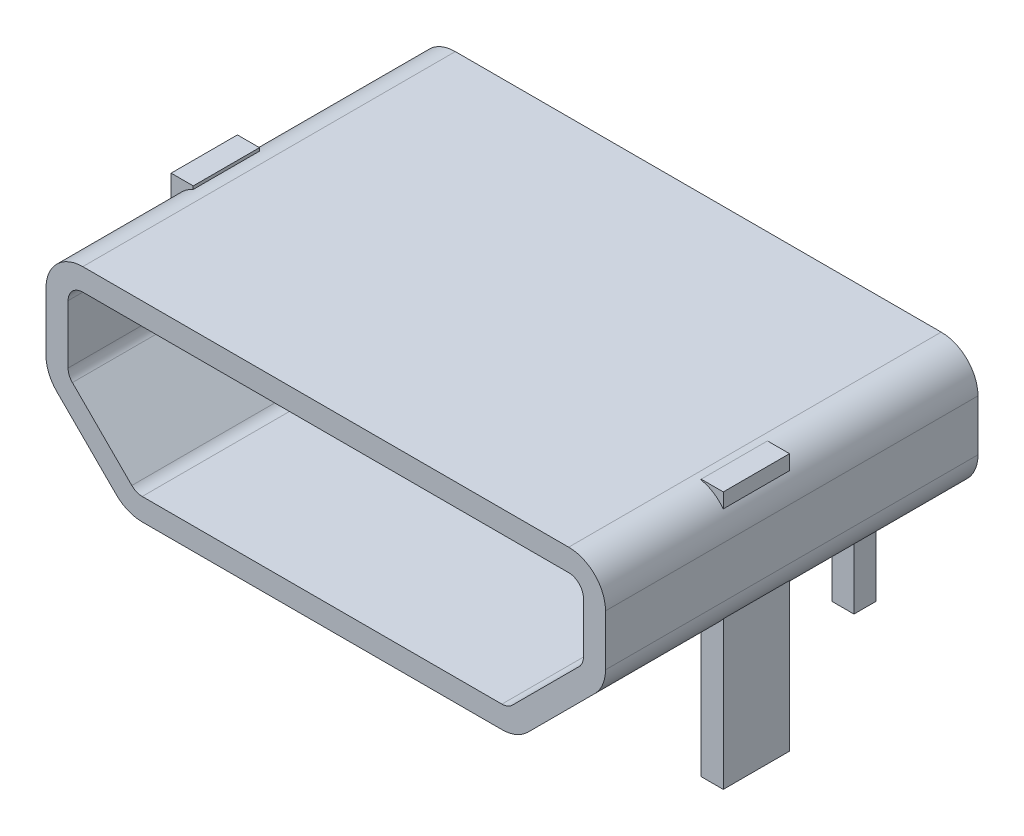
SolidWorks part; units mm, degrees
ref_plane "前视基准面" through (0, 0, 0) normal (0, 0, 1) x (1, 0, 0)
ref_plane "上视基准面" through (0, 0, 0) normal (0, 1, 0) x (1, 0, 0)
ref_plane "右视基准面" through (0, 0, 0) normal (1, 0, 0) x (0, 0, -1)
sketch "草图1" plane through (0, 0, 0) normal (0, 0, 1) x (1, 0, 0)
  line L0 (-3.6036, 0.9536) -> (-2.7964, 0.1464)
  line L1 (-2.4429, 0) -> (2.4429, 0)
  line L2 (-3.75, 1.3071) -> (-3.75, 2.1)
  line L3 (-3.25, 2.6) -> (3.35, 2.6)
  line L4 (3.85, 1.4071) -> (3.85, 2.1)
  line L5 (2.7964, 0.1464) -> (3.7036, 1.0536)
  arc A0 (3.7036, 1.0536) -> (3.85, 1.4071) centre (3.35, 1.4071) ccw
  arc A1 (2.7964, 0.1464) -> (2.4429, 0) centre (2.4429, 0.5) cw
  arc A2 (-3.6036, 0.9536) -> (-3.75, 1.3071) centre (-3.25, 1.3071) cw
  arc A3 (-2.7964, 0.1464) -> (-2.4429, 0) centre (-2.4429, 0.5) ccw
  arc A4 (-3.75, 2.1) -> (-3.25, 2.6) centre (-3.25, 2.1) cw
  arc A5 (3.35, 2.6) -> (3.85, 2.1) centre (3.35, 2.1) cw
  point P0 (-3.75, 0)
  point P3 (3.85, 0)
  point P10 (0, 0)
  point P14 (3.85, 1.2)
  point P17 (2.65, 0)
  point P20 (-3.75, 1.1)
  point P23 (-2.65, 0)
  dimension "D3" = 0.5
  dimension "D4" = 0.5
  dimension "D7" = 0.5
  dimension "D8" = 0.5
  dimension "D9" = 0.5
  dimension "D10" = 0.5
  dimension "D1" = 2.6
  dimension "D2" = 7.6
extrude "凸台-拉伸1" add sketch "草图1" along normal blind 5.06
sketch "草图4" plane through (0, 0, 0) normal (0, 0, -1) x (-1, 0, 0)
  line L8 (-2.4429, 0.3) -> (2.4429, 0.3)
  line L9 (-3.55, 2.1) -> (-3.55, 1.4071)
  line L10 (3.25, 2.3) -> (-3.35, 2.3)
  line L11 (3.45, 1.3071) -> (3.45, 2.1)
  line L12 (-2.4429, 0.3) -> (2.4429, 0.3)
  line L13 (-3.55, 2.1) -> (-3.55, 1.4071)
  line L14 (3.25, 2.3) -> (-3.35, 2.3)
  line L15 (3.45, 1.3071) -> (3.45, 2.1)
  line L18 (-3.4914, 1.2657) -> (-2.5843, 0.3586)
  line L19 (-3.4914, 1.2657) -> (-2.5843, 0.3586)
  line L20 (2.5843, 0.3586) -> (3.3914, 1.1657)
  line L21 (2.5843, 0.3586) -> (3.3914, 1.1657)
  arc A6 (-2.5843, 0.3586) -> (-2.4429, 0.3) centre (-2.4429, 0.5) ccw
  arc A7 (-2.5843, 0.3586) -> (-2.4429, 0.3) centre (-2.4429, 0.5) ccw
  arc A8 (-3.55, 1.4071) -> (-3.4914, 1.2657) centre (-3.35, 1.4071) ccw
  arc A9 (-3.55, 1.4071) -> (-3.4914, 1.2657) centre (-3.35, 1.4071) ccw
  arc A10 (-3.35, 2.3) -> (-3.55, 2.1) centre (-3.35, 2.1) ccw
  arc A11 (-3.35, 2.3) -> (-3.55, 2.1) centre (-3.35, 2.1) ccw
  arc A12 (3.45, 2.1) -> (3.25, 2.3) centre (3.25, 2.1) ccw
  arc A13 (3.45, 2.1) -> (3.25, 2.3) centre (3.25, 2.1) ccw
  arc A14 (3.3914, 1.1657) -> (3.45, 1.3071) centre (3.25, 1.3071) ccw
  arc A15 (3.3914, 1.1657) -> (3.45, 1.3071) centre (3.25, 1.3071) ccw
  arc A16 (2.4429, 0.3) -> (2.5843, 0.3586) centre (2.4429, 0.5) ccw
  arc A17 (2.4429, 0.3) -> (2.5843, 0.3586) centre (2.4429, 0.5) ccw
  dimension "D1" = 0.3
extrude "切除-拉伸1" cut sketch "草图4" against normal up to next
sketch "草图2" plane through (0, 2.6, 0) normal (0, 1, 0) x (1, 0, 0)
  line L0 (0, 0) -> (0, -50000) construction
  line L1 (-2.575, -0.11) -> (-2.275, -0.11)
  line L2 (-2.575, -0.11) -> (-2.575, -0.41)
  line L3 (-2.575, -0.41) -> (-2.275, -0.41)
  line L4 (-2.275, -0.11) -> (-2.275, -0.41)
  line L5 (-2.575, -0.11) -> (-2.275, -0.41) construction
  line L6 (-2.575, -0.41) -> (-2.275, -0.11) construction
  line L7 (-3.75, -5.06) -> (-3.75, 0) construction
  line L8 (-3.75, -3.36) -> (-3.45, -3.36)
  line L9 (-3.75, -3.36) -> (-3.75, -2.46)
  line L10 (-3.75, -2.46) -> (-3.45, -2.46)
  line L11 (-3.45, -3.36) -> (-3.45, -2.46)
  line L12 (-3.75, -3.36) -> (-3.45, -2.46) construction
  line L13 (-3.75, -2.46) -> (-3.45, -3.36) construction
  line L14 (3.75, -2.46) -> (3.45, -3.36) construction
  line L15 (3.75, -3.36) -> (3.45, -2.46) construction
  line L16 (2.575, -0.41) -> (2.275, -0.11) construction
  line L17 (2.575, -0.11) -> (2.275, -0.41) construction
  line L18 (3.45, -3.36) -> (3.45, -2.46)
  line L19 (3.75, -2.46) -> (3.45, -2.46)
  line L20 (3.75, -3.36) -> (3.75, -2.46)
  line L21 (3.75, -3.36) -> (3.45, -3.36)
  line L22 (2.275, -0.11) -> (2.275, -0.41)
  line L23 (2.575, -0.41) -> (2.275, -0.41)
  line L24 (2.575, -0.11) -> (2.575, -0.41)
  line L25 (2.575, -0.11) -> (2.275, -0.11)
  line L26 (3.35, -5.06) -> (-3.25, -5.06) construction
  point P4 (-2.425, -0.26)
  point P12 (-3.6, -2.91)
  point P23 (3.6, -2.91)
  point P24 (2.425, -0.26)
  dimension "D1" = 0.3
  dimension "D2" = 0.3
  dimension "D3" = 0.3
  dimension "D4" = 0.9
  dimension "D5" = 4.85
  dimension "D6" = 4.8
  dimension "D7" = 2.6
extrude "凸台-拉伸2" add sketch "草图2" against normal blind 3.5
